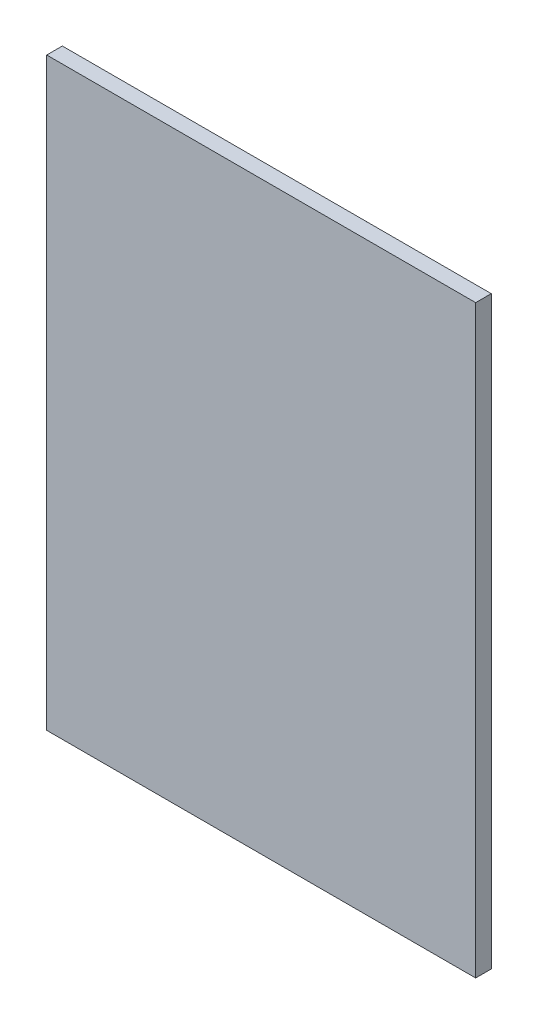
SolidWorks part; units mm, degrees
ref_plane "Front Plane" through (0, 0, 0) normal (0, 0, 1) x (1, 0, 0)
ref_plane "Top Plane" through (0, 0, 0) normal (0, 1, 0) x (1, 0, 0)
ref_plane "Right Plane" through (0, 0, 0) normal (1, 0, 0) x (0, 0, -1)
sketch "Sketch1" plane through (0, 0, 0) normal (0, 0, 1) x (1, 0, 0)
  line L1 (0, 0) -> (110, 0)
  line L2 (0, 0) -> (0, 150)
  line L3 (0, 150) -> (110, 150)
  line L4 (110, 0) -> (110, 150)
  dimension "D1" = 150
  dimension "D2" = 110
extrude "Boss-Extrude1" add sketch "Sketch1" along normal blind 4
